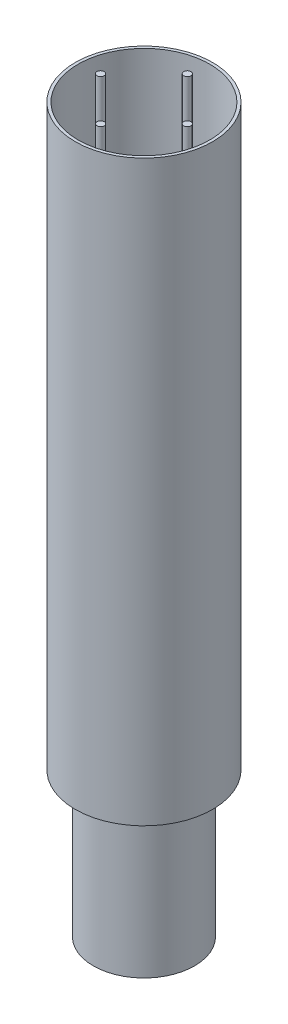
SolidWorks part; units mm, degrees
ref_plane "Front Plane" through (0, 0, 0) normal (0, 0, 1) x (1, 0, 0)
ref_plane "Top Plane" through (0, 0, 0) normal (0, 1, 0) x (1, 0, 0)
ref_plane "Right Plane" through (0, 0, 0) normal (1, 0, 0) x (0, 0, -1)
sketch "Sketch1" plane through (0, 0, 0) normal (0, 1, 0) x (1, 0, 0)
  circle A0 centre (0, 0) radius 35
  dimension "D1" = 70
extrude "Boss-Extrude1" add sketch "Sketch1" along normal blind 100
sketch "Sketch2" plane through (0, 100, 0) normal (0, 1, 0) x (1, 0, 0)
  circle A0 centre (0, 0) radius 47.5
  dimension "D1" = 95
extrude "Boss-Extrude2" add sketch "Sketch2" along normal blind 400
shell "Shell1" thickness 2
sketch "Sketch3" plane through (0, 102, 0) normal (0, 1, 0) x (1, 0, 0)
  circle A0 centre (-30, 0) radius 2.5
  circle A1 centre (0, 30) radius 2.5
  circle A2 centre (30, 0) radius 2.5
  circle A3 centre (0, -30) radius 2.5
  point P11 (0, 0)
  dimension "D1" = 5
  dimension "D2" = 30
  dimension "D3" = 4
extrude "Boss-Extrude3" add sketch "Sketch3" along normal blind 400
